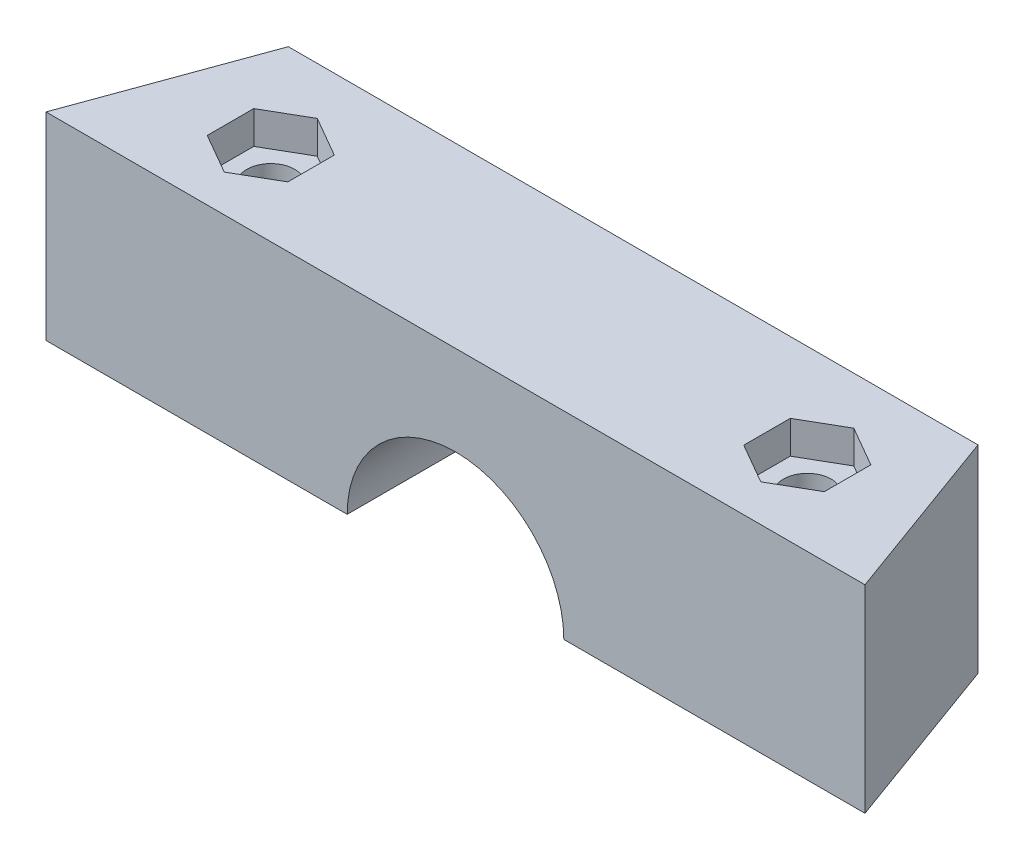
SolidWorks part; units mm, degrees
ref_plane "Front Plane" through (0, 0, 0) normal (0, 0, 1) x (1, 0, 0)
ref_plane "Top Plane" through (0, 0, 0) normal (0, 1, 0) x (1, 0, 0)
ref_plane "Right Plane" through (0, 0, 0) normal (1, 0, 0) x (0, 0, -1)
sketch "Sketch6" plane through (0, 0, 0) normal (0, 1, 0) x (1, 0, 0)
  line L0 (-21.8369, -7.954) -> (8.1631, -7.954)
  line L1 (8.1631, -7.954) -> (23.1631, -49.1662)
  line L2 (23.1631, -49.1662) -> (-36.8369, -49.1662)
  line L3 (-36.8369, -49.1662) -> (-21.8369, -7.954)
  circle A0 centre (8.1631, -18.954) radius 1.78
  circle A1 centre (-21.8369, -18.954) radius 1.78
  circle A2 centre (-26.4869, -43.0491) radius 1.78
  circle A3 centre (12.8131, -72.8149) radius 1.78
  dimension "D1" = 3.56
  dimension "D3" = 3.56
  dimension "D4" = 3.56
  dimension "D5" = 3.56
  dimension "D2" = 60
  dimension "D6" = 30
  dimension "D7" = 11
  dimension "D8" = 11
  dimension "D9" = 49.3
  dimension "D10" = 10.35
  dimension "D11" = 10.35
  dimension "D12" = 30
  dimension "D13" = 70
  dimension "D14" = 110
extrude "Boss-Extrude3" add sketch "Sketch6" along normal blind 14.5 contours L3 L0 L1 L2
sketch "Sketch8" plane through (0, 0, 49.1662) normal (0, 0, 1) x (1, 0, 0)
  line L0 (23.1631, 0) -> (-36.8369, 0) construction
  circle A0 centre (-6.8369, 0) radius 7.935
  dimension "D1" = 15.87
extrude "Cut-Extrude3" cut sketch "Sketch8" against normal blind 88
sketch "Sketch16" plane through (0, 14.5, 0) normal (0, 1, 0) x (1, 0, 0)
  line L0 (-36.8369, -49.1662) -> (-21.8369, -7.954) construction
  line L1 (-26.4897, -46.4526) -> (-23.5397, -44.7494)
  line L2 (-23.5397, -44.7494) -> (-23.5397, -41.343)
  line L3 (-23.5397, -41.343) -> (-26.4897, -39.6398)
  line L4 (-26.4897, -39.6398) -> (-29.4397, -41.343)
  line L5 (-29.4397, -41.343) -> (-29.4397, -44.7494)
  line L6 (-29.4397, -44.7494) -> (-26.4897, -46.4526)
  line L7 (12.8159, -46.4526) -> (15.7659, -44.7494)
  line L8 (15.7659, -44.7494) -> (15.7659, -41.343)
  line L9 (15.7659, -41.343) -> (12.8159, -39.6398)
  line L10 (12.8159, -39.6398) -> (9.8659, -41.343)
  line L11 (9.8659, -41.343) -> (9.8659, -44.7494)
  line L12 (9.8659, -44.7494) -> (12.8159, -46.4526)
  line L13 (23.1631, -49.1662) -> (-36.8369, -49.1662) construction
  line L16 (8.1631, -7.954) -> (23.1631, -49.1662) construction
  circle A0 centre (-26.4897, -43.0462) radius 2.95 construction
  circle A1 centre (12.8159, -43.0462) radius 2.95 construction
  point P20 (0, 0)
  point P21 (0, 0)
  point P22 (0, 0)
  dimension "D1" = 7.63
  dimension "D2" = 6.12
  dimension "D3" = 7.63
  dimension "D4" = 6.12
  dimension "D5" = 5.9
  dimension "D6" = 5.9
extrude "Cut-Extrude7" cut sketch "Sketch16" against normal blind 2.4
sketch "Sketch17" plane through (0, 0, 0) normal (0, -1, 0) x (1, 0, 0)
  line L1 (-26.4897, 39.6398) -> (-23.5397, 41.343)
  line L2 (-23.5397, 41.343) -> (-23.5397, 44.7494)
  line L3 (-23.5397, 44.7494) -> (-26.4897, 46.4526)
  line L4 (-26.4897, 46.4526) -> (-29.4397, 44.7494)
  line L5 (-29.4397, 44.7494) -> (-29.4397, 41.343)
  line L6 (-29.4397, 41.343) -> (-26.4897, 39.6398)
  line L15 (12.8159, 39.6398) -> (15.7659, 41.343)
  line L16 (15.7659, 41.343) -> (15.7659, 44.7494)
  line L17 (15.7659, 44.7494) -> (12.8159, 46.4526)
  line L18 (12.8159, 46.4526) -> (9.8659, 44.7494)
  line L19 (9.8659, 44.7494) -> (9.8659, 41.343)
  line L20 (9.8659, 41.343) -> (12.8159, 39.6398)
  circle A0 centre (-26.4897, 43.0462) radius 2.95 construction
  circle A1 centre (12.8159, 43.0462) radius 2.95 construction
  point P10 (14.2909, 40.4914)
  dimension "D1" = 5.9
  dimension "D2" = 5.9
extrude "Cut-Extrude8" cut sketch "Sketch17" against normal blind 2.4
hole_wizard "Ø1.0mm Dowel Hole1" positions "3DSketch2" profile "Sketch19" hole size "Ø1.0" standard "ANSI Metric" end condition through all
sketch3d "3DSketch2"
  point P0 (-26.4897, 14.5, 43.0462)
  point P3 (12.8159, 14.5, 43.0462)
sketch "Sketch19" plane through (-26.4897, 14.5, 43.0462) normal (1, 0, 0) x (0, 0, 1)
  line L0 (0, 0) -> (0, 14.5)
  line L1 (0, 14.5) -> (1.75, 14.5)
  line L2 (1.75, 14.5) -> (1.75, 0)
  line L5 (1.75, 0) -> (0, 0)
  line L11 (0, -6.35) -> (0, 107.95) construction
  dimension "Thru Hole Dia." = 3.5
  dimension "Thru Hole Depth" = 14.5
sketch "Sketch20" plane through (0, 14.5, 0) normal (0, 1, 0) x (1, 0, 0)
  line L0 (-32.0993, -36.1498) -> (18.4255, -36.1498)
  line L1 (-36.8369, -49.1662) -> (-21.8369, -7.954) construction
  line L2 (8.1631, -7.954) -> (23.1631, -49.1662) construction
  line L3 (18.4255, -36.1498) -> (8.1631, -7.954)
  line L4 (8.1631, -7.954) -> (-21.8369, -7.954)
  line L5 (-21.8369, -7.954) -> (-32.0993, -36.1498)
  dimension "D1" = 3.49
extrude "Cut-Extrude10" cut sketch "Sketch20" against normal blind 22.4
